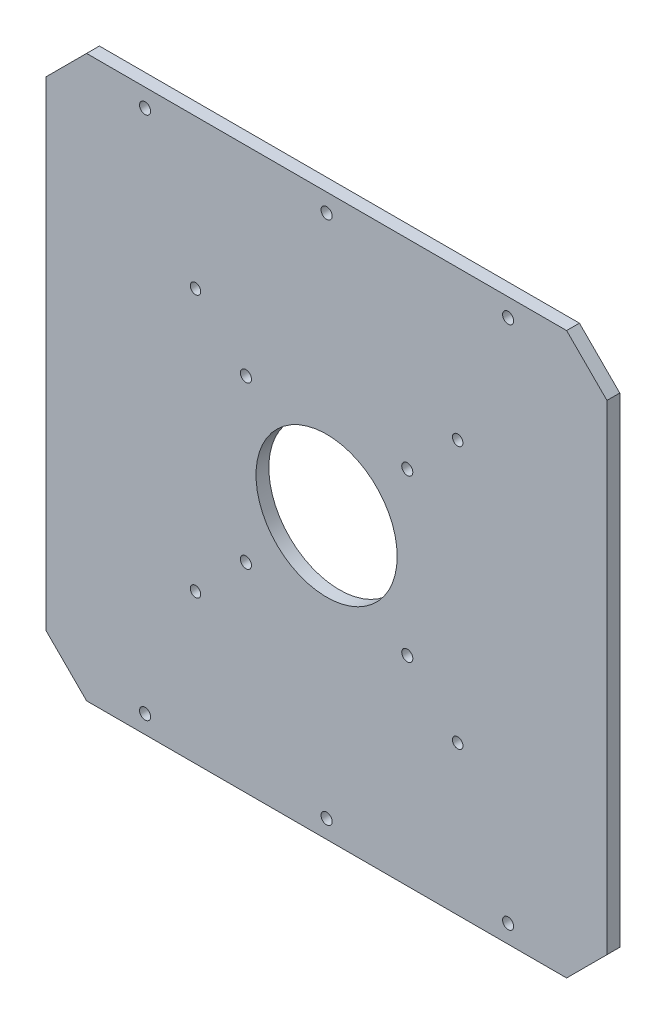
SolidWorks part; units mm, degrees
ref_plane "Front Plane" through (0, 0, 0) normal (0, 0, 1) x (1, 0, 0)
ref_plane "Top Plane" through (0, 0, 0) normal (0, 1, 0) x (1, 0, 0)
ref_plane "Right Plane" through (0, 0, 0) normal (1, 0, 0) x (0, 0, -1)
sketch "Sketch1" plane through (0, 0, 0) normal (0, 0, 1) x (1, 0, 0)
  line L0 (-79.0045, 0) -> (94.053, 0) construction
  line L1 (0, 67.0127) -> (0, -68.6587) construction
  line L3 (139, -139) -> (-139, -139)
  line L4 (139, -139) -> (139, 139)
  line L5 (139, 139) -> (-139, 139)
  line L6 (-139, -139) -> (-139, 139)
  line L7 (139, -139) -> (-139, 139) construction
  line L8 (139, 139) -> (-139, -139) construction
  point P4 (0, 0)
  dimension "D1" = 278
  dimension "D2" = 278
extrude "Boss-Extrude1" add sketch "Sketch1" along normal blind 6.35
sketch "Sketch2" plane through (0, 0, 6.35) normal (0, 0, 1) x (1, 0, 0)
  line L0 (-156.6091, 0) -> (177.3719, 0) construction
  line L1 (0, 110.6274) -> (0, -105.2428) construction
  circle A0 centre (0, 0) radius 35
  circle A1 centre (-40, 40) radius 2.75
  circle A2 centre (40, 40) radius 2.75
  circle A3 centre (40, -40) radius 2.75
  circle A4 centre (-40, -40) radius 2.75
  dimension "D1" = 40
  dimension "D2" = 5.5
  dimension "D3" = 70
  dimension "D4" = 40
extrude "Cut-Extrude1" cut sketch "Sketch2" against normal through all
chamfer "Chamfer1" distance 20 angle 45 4 edges at (139, -139, 3.175) (139, 139, 3.175) (-139, 139, 3.175) (-139, -139, 3.175)
sketch "Sketch4" plane through (0, 0, 6.35) normal (0, 0, 1) x (1, 0, 0)
  line L0 (0, 186.846) -> (0, -174.5938) construction
  line L1 (219.7737, 0) -> (-232.7917, 0) construction
  line L2 (119, 139) -> (-119, 139) construction
  line L3 (-90, -130) -> (0, -130) construction
  circle A0 centre (-90, 130) radius 2.75
  circle A1 centre (0, 130) radius 2.75
  circle A2 centre (90, 130) radius 2.75
  circle A3 centre (90, -130) radius 2.75
  circle A4 centre (0, -130) radius 2.75
  circle A5 centre (-90, -130) radius 2.75
  dimension "D1" = 5.5
  dimension "D2" = 9
  dimension "D3" = 90
extrude "Cut-Extrude2" cut sketch "Sketch4" against normal blind 76.2
sketch "Sketch6" plane through (0, 0, 0) normal (0, 0, -1) x (-1, 0, 0)
  line L0 (0, 163.9888) -> (0, -189.1964) construction
  line L1 (150.9029, 0) -> (-165.98, 0) construction
  circle A0 centre (65, 65) radius 2.6
  circle A1 centre (65, -65) radius 2.6
  circle A2 centre (-65, -65) radius 2.6
  circle A3 centre (-65, 65) radius 2.6
  dimension "D1" = 65
  dimension "D2" = 65
extrude "Cut-Extrude4" cut sketch "Sketch6" against normal through all
equation "\"plate_thickness\" = 6.35 'thickness of the plate "
equation "\"height\"= 180"
equation "\"D1@Boss-Extrude1\"=\"plate_thickness\""
equation "\"t_height\" = 200"
equation "\"t_width\" = 240"
equation "\"t_length\" = 240"
equation "\"plate_spacing\" = 1"
equation "\"front_plate_height\" = \"t_height\" + 38"
equation "\"front_plate_width\" = \"t_width\" + 38"
equation "\"side_plate_height\" = \"front_plate_height\""
equation "\"side_plate_length\" = \"t_length\" + 38"
equation "\"top_plate_width\" = \"front_plate_width\""
equation "\"top_plate_length\" = \"side_plate_length\""
equation "\"D2@Sketch1\"=\"top_plate_width\""
equation "\"D1@Sketch1\"=\"top_plate_length\""
equation "\"plate_hole_spacing\"= 9"
equation "\"connector_D1\" = 70 'the big holes diameter"
equation "\"connector_mtg_D2\"= 5.5 'mounting holes"
equation "\"mtg_dfc\" = 40 'mounting hole distance from center"
equation "\"D3@Sketch2\"=\"connector_D1\""
equation "\"D2@Sketch2\"=\"mtg_hole_D\""
equation "\"D4@Sketch2\"=\"mtg_dfc\""
equation "\"D1@Sketch2\"=\"mtg_dfc\""
equation "\"mtg_hole_D\" = 5.5 'mounting holes"
equation "\"plate_hole_from_edge\" = 9"
equation "\"D1@Sketch4\"=\"mtg_hole_D\""
equation "\"D2@Sketch4\"=\"plate_hole_from_edge\""
equation "\"itx_support_t_slot_length\" = \"t_width\" + (2 * 20.5)"
equation "\"locomotion_length\" = \"t_length\""
equation "\"locomotion_width\" = \"t_width\""
equation "\"locomotion_height\" = 40"
equation "\"itx_mtg_hole_spacing\" = 40"
equation "\"emg30_bracket_hole_len\" = 60"
equation "\"emg30_bracket_hole_wid\" = 11"
equation "\"perce_t_height\" = 50"
equation "\"perce_top_width\" = 150"
equation "\"perce_mtg_hole_spacing\" = \"perce_top_width\" - 20"
equation "\"D1@Sketch6\"=\"perce_mtg_hole_spacing\"/2"
equation "\"D2@Sketch6\"=\"perce_mtg_hole_spacing\"/2"
